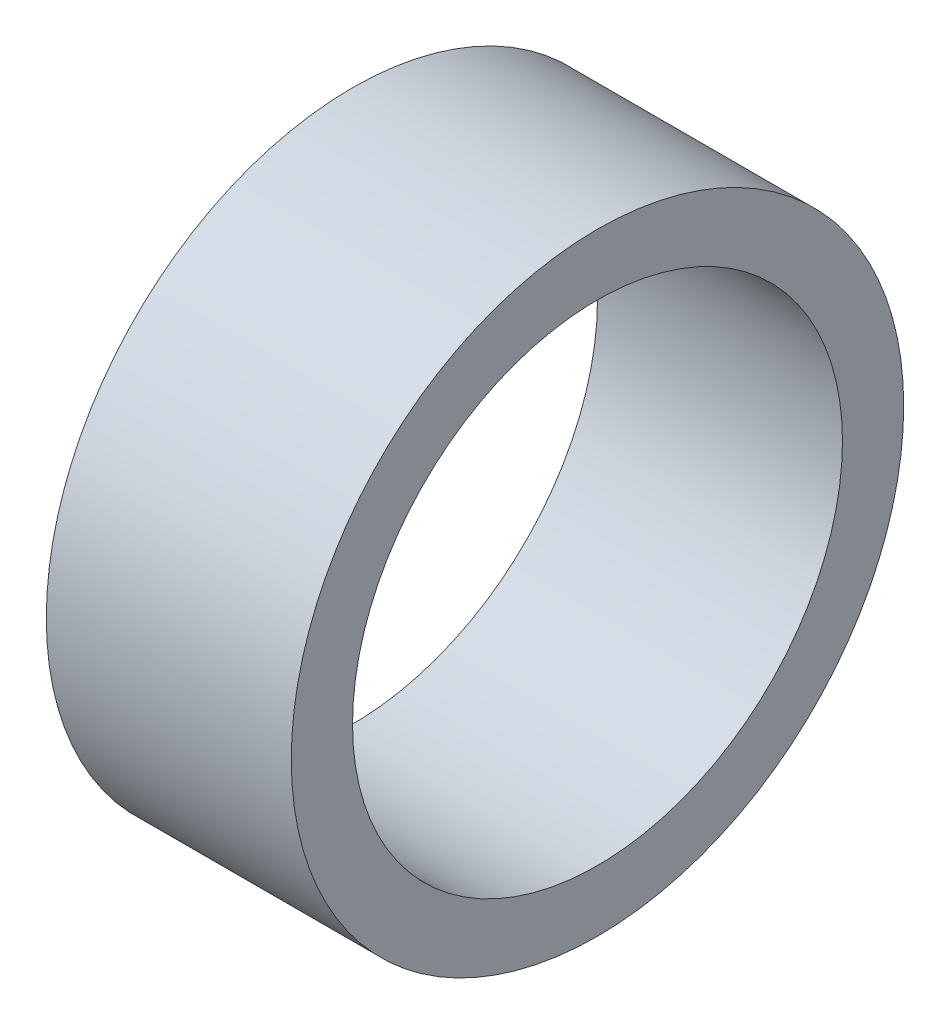
SolidWorks part; units mm, degrees
ref_plane "정면" through (0, 0, 0) normal (0, 0, 1) x (1, 0, 0)
ref_plane "윗면" through (0, 0, 0) normal (0, 1, 0) x (1, 0, 0)
ref_plane "우측면" through (0, 0, 0) normal (1, 0, 0) x (0, 0, -1)
sketch "스케치1" plane through (0, 0, 0) normal (1, 0, 0) x (0, 0, -1)
  circle A0 centre (0, 0) radius 5
  circle A1 centre (0, 0) radius 6.25
  dimension "D1" = 10
  dimension "D2" = 12.5
extrude "보스-돌출1" add sketch "스케치1" along normal blind 5
